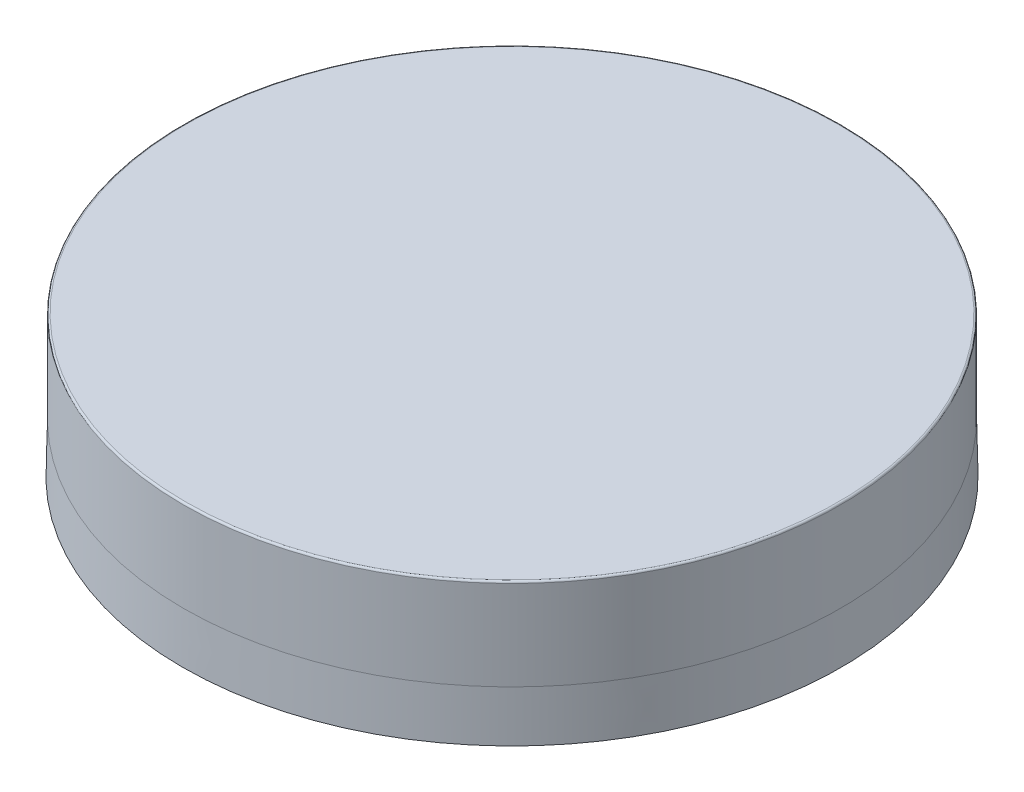
SolidWorks part; units mm, degrees
material "Nylon 6/6 N66-1800 SUPERTOUGH"
ref_plane "Front Plane" through (0, 0, 0) normal (0, 0, 1) x (1, 0, 0)
ref_plane "Top Plane" through (0, 0, 0) normal (0, 1, 0) x (1, 0, 0)
ref_plane "Right Plane" through (0, 0, 0) normal (1, 0, 0) x (0, 0, -1)
sketch "Sketch1" plane through (0, 0, 0) normal (0, 0, 1) x (1, 0, 0)
  line L0 (0, 0) -> (0, 19.304) construction
  line L1 (0, 19.304) -> (-44.45, 19.304)
  line L2 (-44.704, 19.05) -> (-44.704, 6.858)
  line L3 (-44.704, 6.858) -> (-44.8469, 0)
  line L4 (-44.8469, 0) -> (-42.0688, 0)
  line L5 (-41.3486, 1.1275) -> (-43.1064, 4.9213)
  line L6 (-43.18, 5.255) -> (-43.18, 8.0962)
  line L7 (-42.926, 17.78) -> (0, 17.78)
  line L8 (0, 17.78) -> (0, 19.304)
  line L9 (-42.3862, 8.89) -> (-41.0686, 8.89)
  line L10 (-40.4247, 10.1479) -> (-43.0301, 13.7621)
  line L11 (-43.18, 14.2263) -> (-43.18, 17.526)
  line L12 (-43.18, 13.97) -> (-43.18, 8.89) construction
  line L13 (-43.18, 5.08) -> (-43.18, 0) construction
  line L14 (-43.18, 8.0962) -> (-44.704, 8.0962) construction
  arc A0 (-44.45, 19.304) -> (-44.704, 19.05) centre (-44.45, 19.05) ccw
  arc A1 (-42.0688, 0) -> (-41.3486, 1.1275) centre (-42.0688, 0.7938) ccw
  arc A3 (-41.0686, 8.89) -> (-40.4247, 10.1479) centre (-41.0686, 9.6837) ccw
  arc A4 (-43.18, 17.526) -> (-42.926, 17.78) centre (-42.926, 17.526) cw
  arc A5 (-43.1064, 4.9213) -> (-43.18, 5.255) centre (-42.3862, 5.255) cw
  arc A6 (-42.3862, 8.89) -> (-43.18, 8.0962) centre (-42.3862, 8.0962) ccw
  arc A7 (-43.0301, 13.7621) -> (-43.18, 14.2263) centre (-42.3862, 14.2263) cw
  point P16 (-41.3998, 0.3665)
  dimension "D1" = 0.254
  dimension "D5" = 82.55
  dimension "D7" = 89.408
  dimension "D8" = 0.7937
  dimension "D9" = 5.08
  dimension "D12" = 8.89
  dimension "D13" = 4.572
  dimension "D14" = 0.254
  dimension "D15" = 0.7937
  dimension "D2" = 19.304
  dimension "D3" = 89.6938
  dimension "D4" = 6.858
  dimension "D6" = 3.447
  dimension "D10" = 17.78
revolve "Revolve1" add sketch "Sketch1" angle 360 about L0
equation "\"UoM Calc\"= \"PKG COST@01\" / \"PKG QTY@01\""
